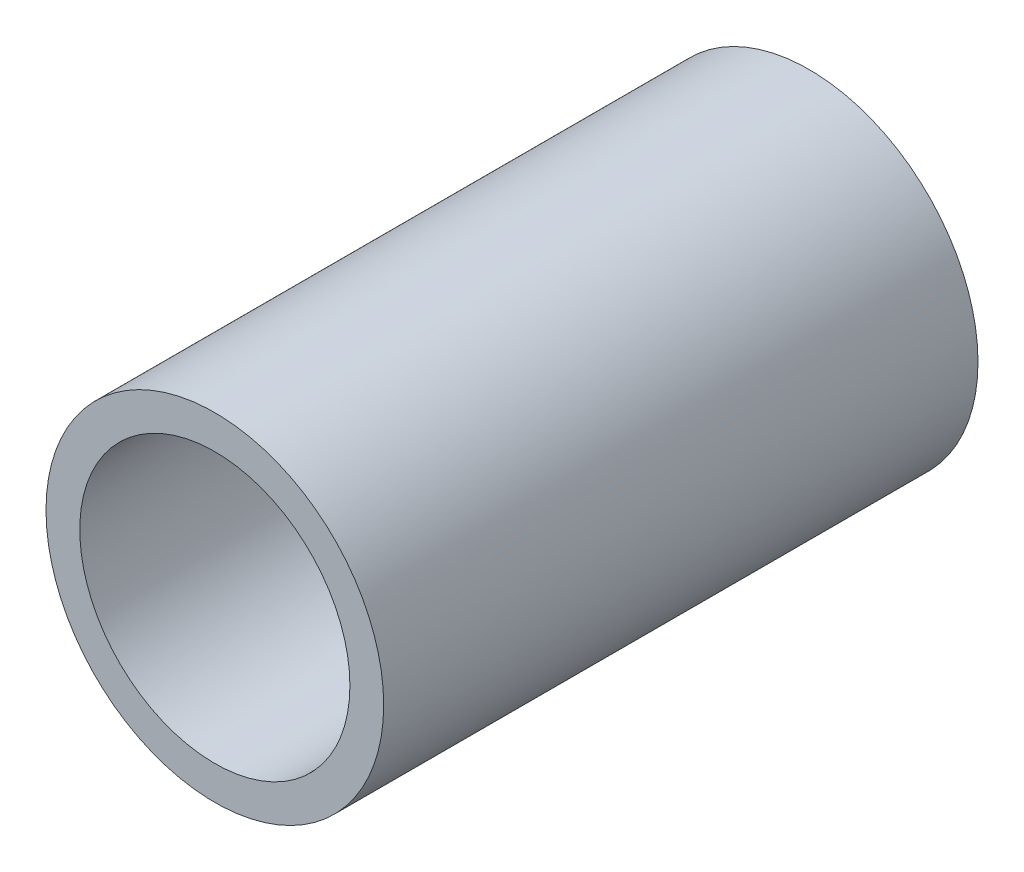
SolidWorks part; units mm, degrees
material "Bronce de aluminio"
ref_plane "Alzado" through (0, 0, 0) normal (0, 0, 1) x (1, 0, 0)
ref_plane "Planta" through (0, 0, 0) normal (0, 1, 0) x (1, 0, 0)
ref_plane "Vista lateral" through (0, 0, 0) normal (1, 0, 0) x (0, 0, -1)
sketch "Croquis2" plane through (0, 0, 0) normal (0, 0, 1) x (1, 0, 0)
  circle A0 centre (0, 0) radius 43.75
  circle A1 centre (0, 0) radius 35
  dimension "D1" = 87.5
  dimension "D2" = 70
extrude "Saliente-Extruir6" add sketch "Croquis2" along normal blind 154
